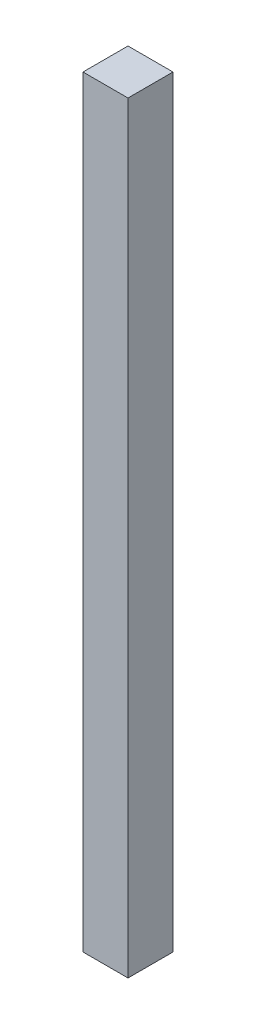
SolidWorks part; units mm, degrees
ref_plane "Front Plane" through (0, 0, 0) normal (0, 0, 1) x (1, 0, 0)
ref_plane "Top Plane" through (0, 0, 0) normal (0, 1, 0) x (1, 0, 0)
ref_plane "Right Plane" through (0, 0, 0) normal (1, 0, 0) x (0, 0, -1)
sketch "Sketch1" plane through (0, 0, 0) normal (0, 1, 0) x (1, 0, 0)
  line L1 (-39.8355, 18.6136) -> (-14.4355, 18.6136)
  line L2 (-39.8355, 18.6136) -> (-39.8355, -6.7864)
  line L3 (-39.8355, -6.7864) -> (-14.4355, -6.7864)
  line L4 (-14.4355, 18.6136) -> (-14.4355, -6.7864)
  dimension "D1" = 25.4
  dimension "D2" = 25.4
extrude "Boss-Extrude1" add sketch "Sketch1" along normal blind 430
